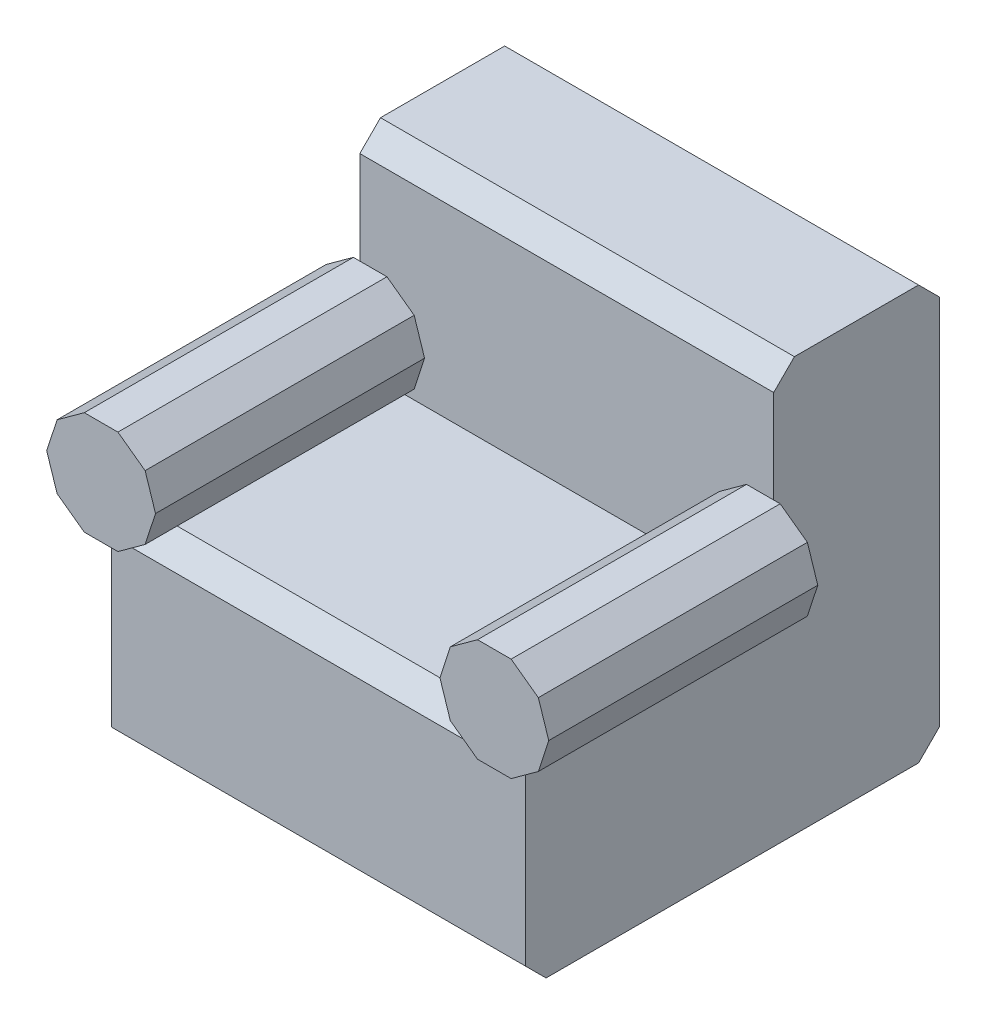
SolidWorks part; units mm, degrees
ref_plane "Front Plane" through (0, 0, 0) normal (0, 0, 1) x (1, 0, 0)
ref_plane "Top Plane" through (0, 0, 0) normal (0, 1, 0) x (1, 0, 0)
ref_plane "Right Plane" through (0, 0, 0) normal (1, 0, 0) x (0, 0, -1)
sketch "Sketch1" plane through (0, 0, 0) normal (1, 0, 0) x (0, 0, -1)
  line L0 (0, 0) -> (-55, 0)
  line L1 (-60, -5) -> (-60, -45)
  line L2 (-55, -50) -> (35, -50)
  line L3 (40, -45) -> (40, 45)
  line L4 (35, 50) -> (5, 50)
  line L5 (0, 45) -> (0, 0)
  line L6 (-55, 0) -> (-60, -5)
  line L7 (5, 50) -> (0, 45)
  line L8 (40, 45) -> (35, 50)
  line L9 (-60, -45) -> (-55, -50)
  line L10 (35, -50) -> (40, -45)
  point P1 (-60, 0)
  point P3 (-60, -50)
  point P4 (40, -50)
  point P5 (40, 50)
  point P6 (0, 50)
  point P17 (40, 0)
  dimension "D1" = 100
  dimension "D2" = 100
  dimension "D8" = 30
extrude "Boss-Extrude1" add sketch "Sketch1" along normal mid plane 100
sketch "Sketch2" plane through (0, 0, 0) normal (0, 0, 1) x (1, 0, 0)
  line L0 (50, 45) -> (50, 0) construction
  line L1 (60.6433, 10) -> (58.1331, 17.7254)
  line L2 (58.1331, 17.7254) -> (51.5615, 22.5)
  line L3 (51.5615, 22.5) -> (43.4385, 22.5)
  line L4 (43.4385, 22.5) -> (36.8669, 17.7254)
  line L5 (36.8669, 17.7254) -> (34.3567, 10)
  line L6 (34.3567, 10) -> (36.8669, 2.2746)
  line L7 (36.8669, 2.2746) -> (43.4385, -2.5)
  line L8 (43.4385, -2.5) -> (51.5615, -2.5)
  line L9 (51.5615, -2.5) -> (58.1331, 2.2746)
  line L10 (58.1331, 2.2746) -> (60.6433, 10)
  circle A0 centre (47.5, 10) radius 12.5 construction
  line M2 (-50, 0) -> (50, 0)
  line M3 (50, 0) -> (50, 45)
  dimension "D2" = 25
  dimension "D1" = 2.5
  dimension "D3" = 10
extrude "Boss-Extrude3" add sketch "Sketch2" along normal offset from surface (65 mm away) 5 contours L5 L6 L2 L3 L4 M2 M3 | L9 L10 L1 L2 L6 L7 L8 M3 M2 up to face at (0, -25, 60) offset beyond the face yes
mirror "Mirror1" about plane through (0, 0, 0) normal (1, 0, 0) of "Boss-Extrude3"
sketch "Sketch5" plane through (0, 0, 0) normal (0, 0, 1) x (1, 0, 0)
  line L0 (-1.25, 0) -> (-1.25, 50)
  line L1 (39.9975, 0) -> (-39.9975, 0) construction
  line L2 (50, 50) -> (-50, 50) construction
  line L3 (-1.25, 50) -> (1.25, 50)
  line L4 (1.25, 50) -> (1.25, 0)
  line L5 (1.25, 0) -> (-1.25, 0)
  point P7 (0, 50)
  dimension "D1" = 2.5
